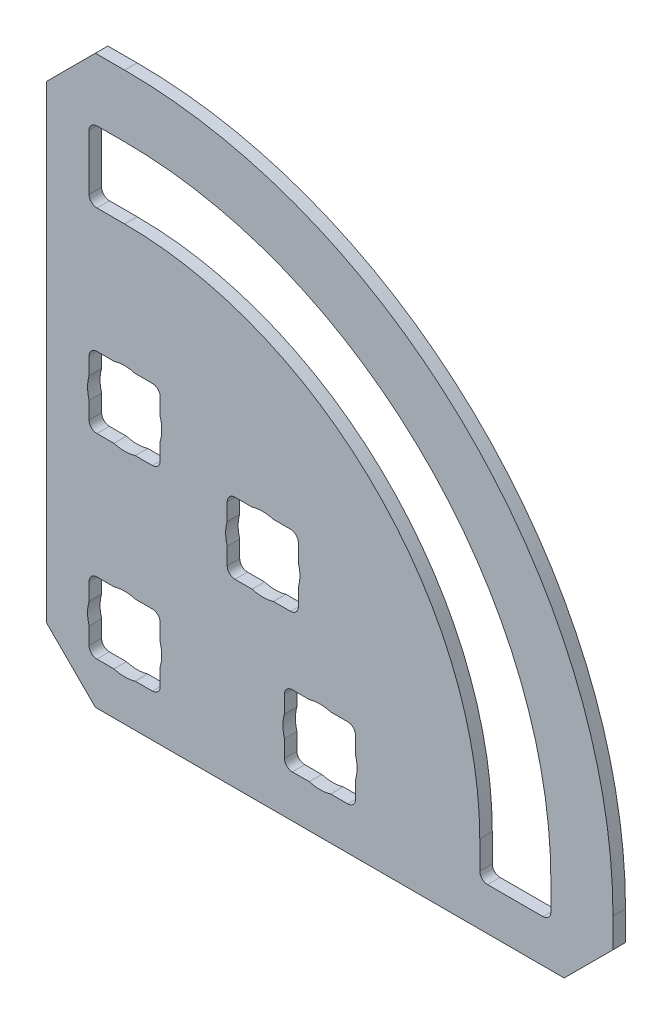
SolidWorks part; units mm, degrees
material "Custom Plastic"
ref_plane "Front Plane" through (0, 0, 0) normal (0, 0, 1) x (1, 0, 0)
ref_plane "Top Plane" through (0, 0, 0) normal (0, 1, 0) x (1, 0, 0)
ref_plane "Right Plane" through (0, 0, 0) normal (1, 0, 0) x (0, 0, -1)
ref_plane "Plane1" through (0, 0, 0.8128) normal (0, 0, 1) x (1, 0, 0)
sketch "Sketch1" plane through (0, 0, 0.8128) normal (0, 0, 1) x (1, 0, 0)
  line L0 (-14.9666, 23.1461) -> (-14.9666, -7.3339)
  line L1 (-14.9666, -7.3339) -> (-11.7916, -10.5089)
  line L2 (-11.7916, -10.5089) -> (18.6884, -10.5089)
  line L3 (18.6884, -10.5089) -> (21.8634, -7.3339)
  line L4 (21.8634, -7.3339) -> (21.8634, -5.4289)
  line L5 (-9.8866, 26.3211) -> (-11.7916, 26.3211)
  line L6 (-11.7916, 26.3211) -> (-14.9666, 23.1461)
  line L7 (17.3168, -7.7403) -> (13.71, -7.7403)
  line L8 (13.202, -7.2323) -> (13.202, -5.4289)
  line L9 (-9.8866, 17.6597) -> (-11.69, 17.6597)
  line L10 (-12.198, 18.1677) -> (-12.198, 21.7745)
  line L11 (-11.69, 22.2825) -> (-9.8866, 22.2825)
  line L12 (17.8248, -5.4289) -> (17.8248, -7.2323)
  line L13 (5.1248, -3.6255) -> (5.1248, -7.2323)
  line L14 (4.6168, -7.7403) -> (1.01, -7.7403)
  line L15 (0.502, -7.2323) -> (0.502, -3.6255)
  line L16 (1.01, -3.1175) -> (4.6168, -3.1175)
  line L17 (-2.7098, 5.8627) -> (0.897, 5.8627)
  line L18 (1.405, 5.3547) -> (1.405, 1.7479)
  line L19 (0.897, 1.2399) -> (-2.7098, 1.2399)
  line L20 (-3.2178, 1.7479) -> (-3.2178, 5.3547)
  line L21 (-11.69, 9.5825) -> (-8.0832, 9.5825)
  line L22 (-7.5752, 9.0745) -> (-7.5752, 5.4677)
  line L23 (-8.0832, 4.9597) -> (-11.69, 4.9597)
  line L24 (-12.198, 5.4677) -> (-12.198, 9.0745)
  line L25 (-8.0832, -7.7403) -> (-11.69, -7.7403)
  line L26 (-12.198, -7.2323) -> (-12.198, -3.6255)
  line L27 (-11.69, -3.1175) -> (-8.0832, -3.1175)
  line L28 (-7.5752, -3.6255) -> (-7.5752, -7.2323)
  arc A0 (21.8634, -5.4289) -> (-9.8866, 26.3211) centre (-9.8866, -5.4289) ccw
  arc A1 (13.71, -7.7403) -> (13.202, -7.2323) centre (13.71, -7.2323) cw
  arc A2 (13.202, -5.4289) -> (-9.8866, 17.6597) centre (-9.8866, -5.4289) ccw
  arc A3 (-11.69, 17.6597) -> (-12.198, 18.1677) centre (-11.69, 18.1677) cw
  arc A4 (-12.198, 21.7745) -> (-11.69, 22.2825) centre (-11.69, 21.7745) cw
  arc A5 (-9.8866, 22.2825) -> (17.8248, -5.4289) centre (-9.8866, -5.4289) cw
  arc A6 (17.8248, -7.2323) -> (17.3168, -7.7403) centre (17.3168, -7.2323) cw
  arc A7 (4.6168, -3.1175) -> (5.1248, -3.6255) centre (4.6168, -3.6255) cw
  arc A8 (5.1248, -7.2323) -> (4.6168, -7.7403) centre (4.6168, -7.2323) cw
  arc A9 (1.01, -7.7403) -> (0.502, -7.2323) centre (1.01, -7.2323) cw
  arc A10 (0.502, -3.6255) -> (1.01, -3.1175) centre (1.01, -3.6255) cw
  arc A11 (-3.2178, 5.3547) -> (-2.7098, 5.8627) centre (-2.7098, 5.3547) cw
  arc A12 (0.897, 5.8627) -> (1.405, 5.3547) centre (0.897, 5.3547) cw
  arc A13 (1.405, 1.7479) -> (0.897, 1.2399) centre (0.897, 1.7479) cw
  arc A14 (-2.7098, 1.2399) -> (-3.2178, 1.7479) centre (-2.7098, 1.7479) cw
  arc A15 (-12.198, 9.0745) -> (-11.69, 9.5825) centre (-11.69, 9.0745) cw
  arc A16 (-8.0832, 9.5825) -> (-7.5752, 9.0745) centre (-8.0832, 9.0745) cw
  arc A17 (-7.5752, 5.4677) -> (-8.0832, 4.9597) centre (-8.0832, 5.4677) cw
  arc A18 (-11.69, 4.9597) -> (-12.198, 5.4677) centre (-11.69, 5.4677) cw
  arc A19 (-7.5752, -7.2323) -> (-8.0832, -7.7403) centre (-8.0832, -7.2323) cw
  arc A20 (-11.69, -7.7403) -> (-12.198, -7.2323) centre (-11.69, -7.2323) cw
  arc A21 (-12.198, -3.6255) -> (-11.69, -3.1175) centre (-11.69, -3.6255) cw
  arc A22 (-8.0832, -3.1175) -> (-7.5752, -3.6255) centre (-8.0832, -3.6255) cw
extrude "Boss-Extrude1" add sketch "Sketch1" against normal blind 0.8128
sketch "Sketch2" plane through (0, 0, 0.8128) normal (0, 0, 1) x (1, 0, 0)
  line L0 (-12.198, 7.2711) -> (-7.5752, 7.2711) construction
  line L1 (-12.198, 9.0745) -> (-12.198, 5.4677) construction
  line L2 (-7.5752, 5.4677) -> (-7.5752, 9.0745) construction
  line L3 (0.897, 5.8627) -> (-2.7098, 5.8627) construction
  line L4 (-0.9064, 5.8627) -> (-0.9064, 1.2399) construction
  line L5 (-2.7098, 1.2399) -> (0.897, 1.2399) construction
  line L7 (-8.0832, -3.1175) -> (-11.69, -3.1175) construction
  line L8 (-9.8866, -3.1175) -> (-9.8866, -7.7403) construction
  line L9 (-11.69, -7.7403) -> (-8.0832, -7.7403) construction
  line L11 (4.6168, -3.1175) -> (1.01, -3.1175) construction
  line L12 (2.8134, -3.1175) -> (2.8134, -7.7403) construction
  line L13 (1.01, -7.7403) -> (4.6168, -7.7403) construction
  circle A0 centre (-9.8866, 7.2711) radius 2.413
  circle A1 centre (-0.9064, 3.5513) radius 2.413
  circle A2 centre (2.8134, -5.4289) radius 2.413
  circle A3 centre (-9.8866, -5.4289) radius 2.413
  dimension "D1" = 4.826
extrude "Cut-Extrude1" cut sketch "Sketch2" against normal blind 2.54
